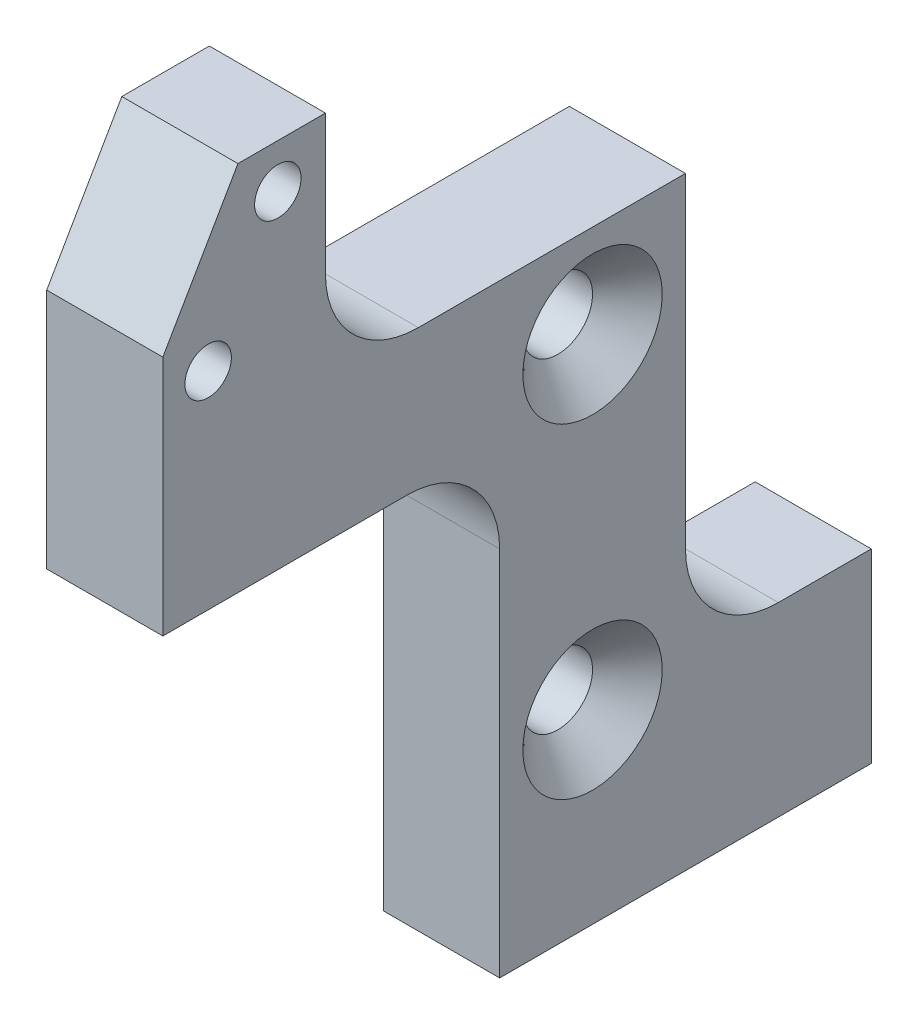
SolidWorks part; units mm, degrees
ref_plane "Front Plane" through (0, 0, 0) normal (0, 0, 1) x (1, 0, 0)
ref_plane "Top Plane" through (0, 0, 0) normal (0, 1, 0) x (1, 0, 0)
ref_plane "Right Plane" through (0, 0, 0) normal (1, 0, 0) x (0, 0, -1)
sketch "Sketch1" plane through (0, 0, 0) normal (1, 0, 0) x (0, 0, -1)
  line L0 (30.5, 0) -> (14.5, 0)
  line L1 (14.5, 0) -> (14.5, 20)
  line L2 (14.5, 20) -> (0, 20)
  line L3 (0, 20) -> (0, 30.4)
  line L4 (0, 30.4) -> (3.2332, 36)
  line L5 (3.2332, 36) -> (7, 36)
  line L6 (7, 36) -> (7, 26)
  line L7 (7, 26) -> (22.5, 26)
  line L8 (22.5, 26) -> (22.5, 8)
  line L9 (22.5, 8) -> (30.5, 8)
  line L10 (30.5, 8) -> (30.5, 0)
  line L11 (1.95, 28.91) -> (4.95, 34.1062) construction
  circle A0 centre (18.5, 8) radius 1.5
  circle A1 centre (18.5, 22) radius 1.5
  circle A2 centre (1.95, 28.91) radius 1
  circle A3 centre (4.95, 34.1062) radius 1
  dimension "D3" = 3
  dimension "D4" = 2
  dimension "D1" = 8
  dimension "D2" = 14.5
  dimension "D5" = 16
  dimension "D6" = 12
  dimension "D7" = 14
  dimension "D8" = 8
  dimension "D9" = 20
  dimension "D10" = 120
  dimension "D11" = 5.6
  dimension "D12" = 6
  dimension "D13" = 1.95
  dimension "D14" = 7.09
  dimension "D15" = 7
  dimension "D16" = 10
  dimension "D17" = 36
extrude "Boss-Extrude1" add sketch "Sketch1" along normal blind 5
fillet "Fillet1" radius 4 3 edges at (2.5, 8, -22.5) (2.5, 20, -14.5) (2.5, 26, -7)
hole_wizard "Tap Drill for M3x0.5 Tap1" positions "Sketch3" profile "Sketch2" hole size "M3x0.5" standard "ANSI Metric"
sketch "Sketch3" plane through (0, 0, 0) normal (0, -1, 0) x (-1, 0, 0)
  line L0 (-5, 14.5) -> (-5, 30.5) construction
  line L1 (-5, 30.5) -> (0, 30.5) construction
  point P0 (-2.5, 17.5)
  point P2 (-2.5, 27.5)
  dimension "D1" = 2.5
  dimension "D2" = 3
  dimension "D3" = 10
sketch "Sketch2" plane through (2.5, 0, -17.5) normal (1, 0, 0) x (0, 0, -1)
  line L0 (0, 0) -> (0, 4)
  line L1 (0, 4) -> (1.25, 4)
  line L2 (1.25, 4) -> (1.25, 0)
  line L5 (1.25, 0) -> (0, 0)
  line L10 (0, 4) -> (-1.25, 4) construction
  line L11 (0, -6.35) -> (0, 107.95) construction
  dimension "Hole Dia." = 2.5
  dimension "Hole Depth" = 4
  dimension "Drill Angle" = 180
chamfer "Chamfer1" distance 1.5 angle 45 2 edges at (5, 8, -20) (5, 22, -20)
